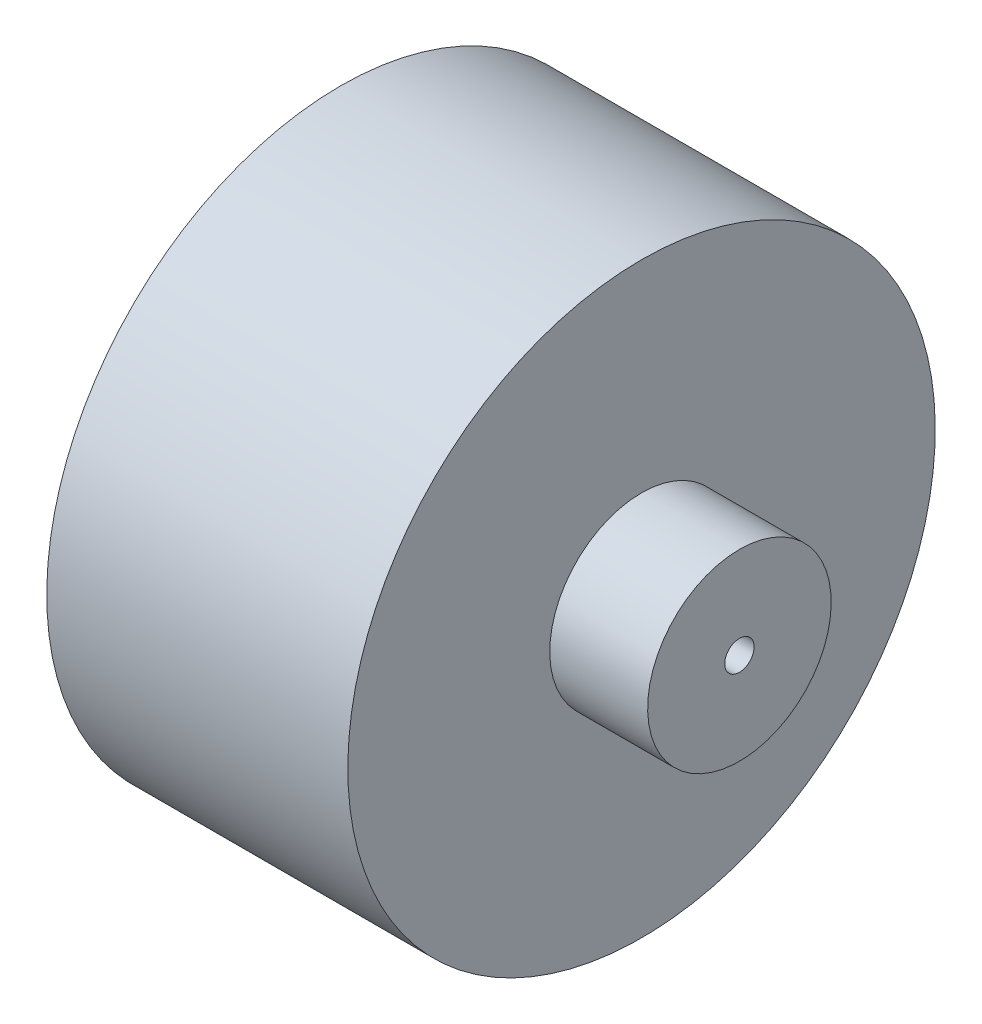
SolidWorks part; units mm, degrees
ref_plane "Front Plane" through (0, 0, 0) normal (0, 0, 1) x (1, 0, 0)
ref_plane "Top Plane" through (0, 0, 0) normal (0, 1, 0) x (1, 0, 0)
ref_plane "Right Plane" through (0, 0, 0) normal (1, 0, 0) x (0, 0, -1)
sketch "Sketch1" plane through (0, 0, 0) normal (0, 0, 1) x (1, 0, 0)
  line L0 (-25, 0) -> (-163, 0)
  line L1 (0, 0) -> (-40.8199, 0) construction
  line L2 (-163, 0) -> (-163, 120)
  line L3 (-163, 120) -> (-40, 120)
  line L4 (-40, 120) -> (-40, 37.5)
  line L5 (-40, 37.5) -> (0, 37.5)
  line L6 (-25, 0) -> (-25, 6)
  line L7 (-25, 6) -> (0, 6)
  line L8 (0, 6) -> (0, 37.5)
  dimension "D1" = 12
  dimension "D2" = 240
  dimension "D3" = 123
  dimension "D4" = 40
  dimension "D5" = 25
  dimension "D6" = 75
revolve "Revolve1" add sketch "Sketch1" angle 360 about L1
